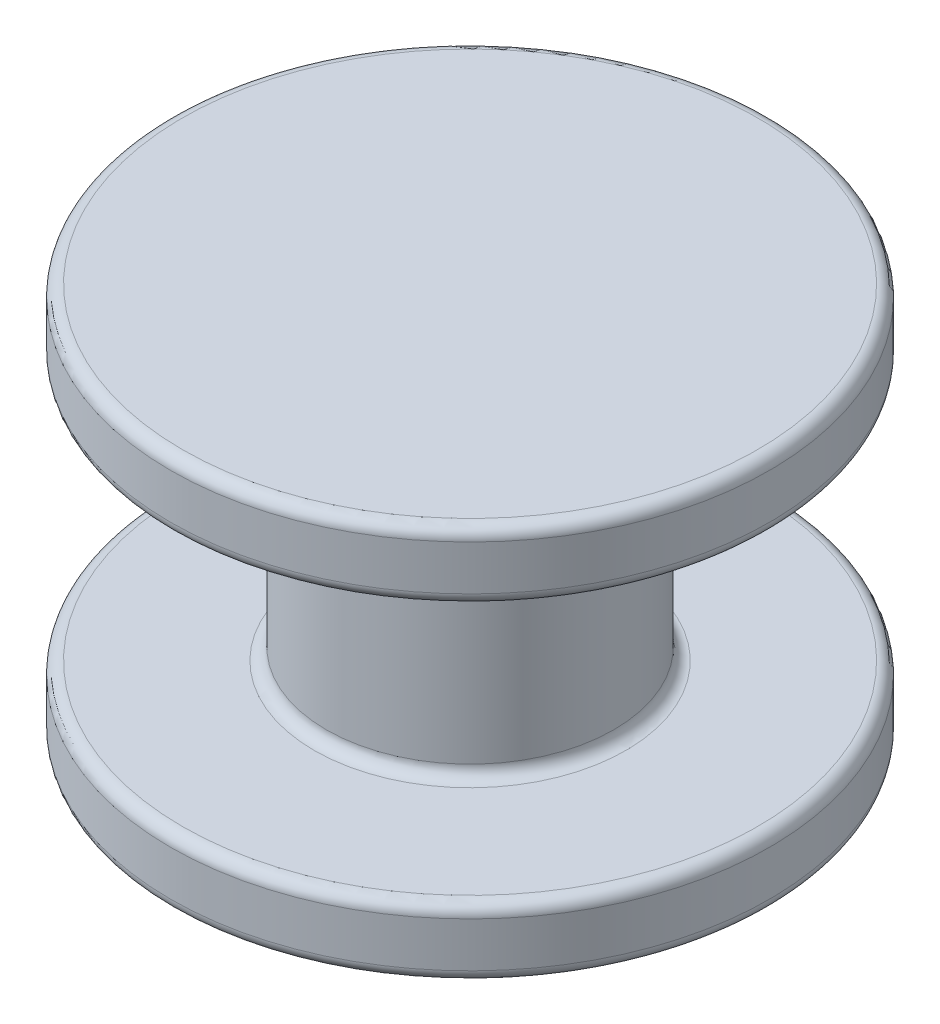
SolidWorks part; units mm, degrees
ref_plane "Front Plane" through (0, 0, 0) normal (0, 0, 1) x (1, 0, 0)
ref_plane "Top Plane" through (0, 0, 0) normal (0, 1, 0) x (1, 0, 0)
ref_plane "Right Plane" through (0, 0, 0) normal (1, 0, 0) x (0, 0, -1)
sketch "Sketch1" plane through (0, 0, 0) normal (0, 1, 0) x (1, 0, 0)
  circle A0 centre (0, 0) radius 5
  dimension "D1" = 10
extrude "Boss-Extrude1" add sketch "Sketch1" along normal blind 1.15
sketch "Sketch2" plane through (0, 1.15, 0) normal (0, 1, 0) x (1, 0, 0)
  circle A0 centre (0, 0) radius 2.4
  dimension "D1" = 4.8
extrude "Boss-Extrude2" add sketch "Sketch2" along normal blind 4.3
sketch "Sketch3" plane through (0, 5.45, 0) normal (0, 1, 0) x (1, 0, 0)
  circle A0 centre (0, 0) radius 5
  circle A1 centre (0, 0) radius 5 construction
extrude "Boss-Extrude3" add sketch "Sketch3" along normal blind 1.15
fillet "Fillet1" radius 0.2 6 edges at (0, 0, 5) (0, 5.45, 2.4) (0, 1.15, 2.4) (0, 1.15, 5) (0, 5.45, 5) (0, 6.6, 5)
